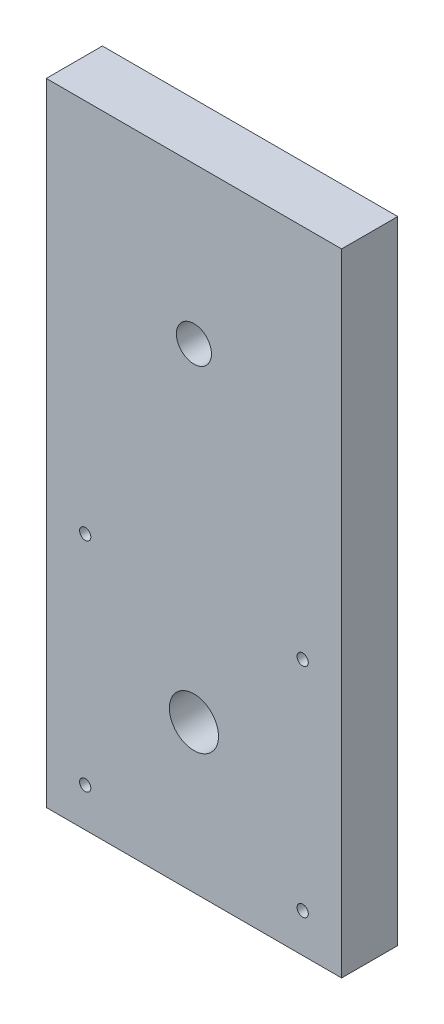
SolidWorks part; units mm, degrees
ref_plane "Front" through (0, 0, 0) normal (0, 0, 1) x (1, 0, 0)
ref_plane "Top" through (0, 0, 0) normal (0, 1, 0) x (1, 0, 0)
ref_plane "Right" through (0, 0, 0) normal (1, 0, 0) x (0, 0, -1)
ref_plane "Plane1" through (0, 0, 0) normal (0, 0, 1) x (1, 0, 0)
sketch "Sketch2" plane through (0, 0, 0) normal (0, 0, 1) x (1, 0, 0)
  line L0 (-17.05, -21.05) -> (17.05, -21.05) construction
  line L1 (21.05, 68.95) -> (-21.05, 68.95)
  line L2 (21.05, 68.95) -> (21.05, -21.05)
  line L3 (21.05, -21.05) -> (-21.05, -21.05)
  line L4 (-21.05, 68.95) -> (-21.05, -21.05)
  line L5 (21.05, -17.05) -> (21.05, 17.05) construction
  line L6 (-21.05, 17.05) -> (-21.05, -17.05) construction
  circle A0 centre (0, 0) radius 11.75
  dimension "D2" = 23.5
  dimension "D1" = 90
extrude "Boss-Extrude1" add sketch "Sketch2" along normal blind 3
sketch "Sketch3" plane through (0, 0, 3) normal (0, 0, 1) x (1, 0, 0)
  line L4 (21.05, -21.05) -> (21.05, 68.95)
  line L5 (21.05, 68.95) -> (-21.05, 68.95)
  line L6 (-21.05, 68.95) -> (-21.05, -21.05)
  line L7 (-21.05, -21.05) -> (21.05, -21.05)
  line L8 (21.05, -21.05) -> (21.05, 68.95)
  line L9 (21.05, 68.95) -> (-21.05, 68.95)
  line L10 (-21.05, 68.95) -> (-21.05, -21.05)
  line L11 (-21.05, -21.05) -> (21.05, -21.05)
  circle A0 centre (0, 0) radius 3.5
  dimension "D2" = 7
  dimension "D1" = 0
extrude "Boss-Extrude2" add sketch "Sketch3" along normal blind 5
sketch "Sketch6" plane through (0, 0, 8) normal (0, 0, 1) x (1, 0, 0)
  circle A0 centre (-15.5, 15.5) radius 0.8 construction
  circle A1 centre (-15.5, -15.5) radius 0.8 construction
  circle A2 centre (15.5, 15.5) radius 0.8 construction
  circle A3 centre (15.5, -15.5) radius 0.8 construction
  circle A4 centre (-15.5, 15.5) radius 0.8
  circle A5 centre (-15.5, -15.5) radius 0.8
  circle A6 centre (15.5, 15.5) radius 0.8
  circle A7 centre (15.5, -15.5) radius 0.8
extrude "Cut-Extrude1" cut sketch "Sketch6" against normal through all
sketch "Sketch7" plane through (0, 0, 8) normal (0, 0, 1) x (1, 0, 0)
  circle A0 centre (0, 46.7079) radius 2.5 construction
  circle A1 centre (0, 46.7079) radius 2.5
extrude "Cut-Extrude2" cut sketch "Sketch7" against normal through all
